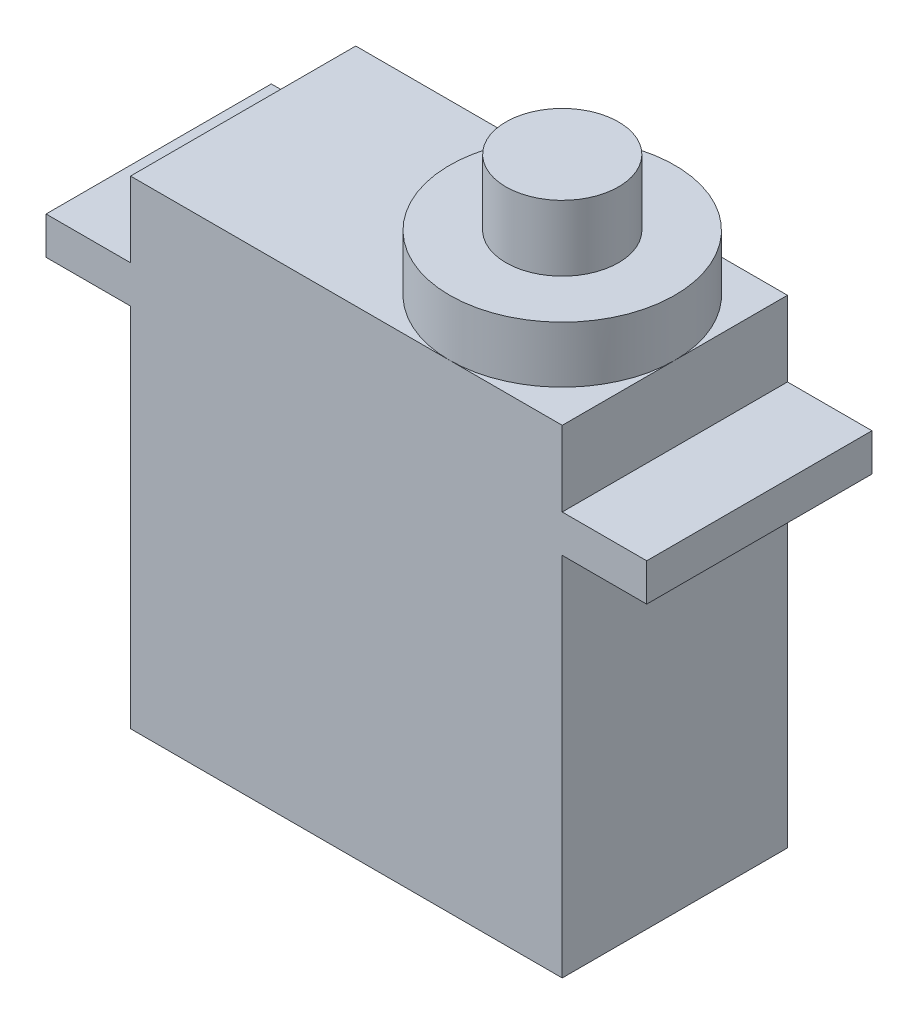
SolidWorks part; units mm, degrees
ref_plane "Front Plane" through (0, 0, 0) normal (0, 0, 1) x (1, 0, 0)
ref_plane "Top Plane" through (0, 0, 0) normal (0, 1, 0) x (1, 0, 0)
ref_plane "Right Plane" through (0, 0, 0) normal (1, 0, 0) x (0, 0, -1)
sketch "Sketch1" plane through (0, 0, 0) normal (0, 1, 0) x (1, 0, 0)
  line L1 (0, 0) -> (23, 0)
  line L2 (0, 0) -> (0, 12)
  line L3 (0, 12) -> (23, 12)
  line L4 (23, 0) -> (23, 12)
extrude "Boss-Extrude1" add sketch "Sketch1" along normal blind 19.5
sketch "Sketch2" plane through (0, 19.5, 0) normal (0, 1, 0) x (1, 0, 0)
  line L0 (11.5, 0) -> (-4.5, 0)
  line L1 (0, 0) -> (23, 0) construction
  line L2 (-4.5, 0) -> (-4.5, 12)
  line L3 (-4.5, 12) -> (27.5, 12)
  line L4 (27.5, 12) -> (27.5, 0)
  line L5 (27.5, 0) -> (0, 0)
  line M1 (0, 12) -> (0, 0)
  line M2 (0, 0) -> (23, 0)
  line M3 (23, 0) -> (23, 12)
  line M4 (23, 12) -> (0, 12)
extrude "Boss-Extrude2" add sketch "Sketch2" along normal blind 2 contours L3 L2 L0 M1 | L5 L4 L3 M3 | M4 M1 M2 M3
sketch "Sketch3" plane through (0, 21.5, 0) normal (0, 1, 0) x (1, 0, 0)
  line L1 (0, 0) -> (23, 0)
  line L2 (0, 0) -> (0, 12)
  line L3 (0, 12) -> (23, 12)
  line L4 (23, 0) -> (23, 12)
extrude "Boss-Extrude3" add sketch "Sketch3" along normal blind 4
sketch "Sketch4" plane through (0, 25.5, 0) normal (0, 1, 0) x (1, 0, 0)
  line L0 (23, 0) -> (11, 0)
  line L1 (0, 0) -> (23, 0) construction
  line L2 (11, 0) -> (11, 12)
  line L3 (23, 12) -> (0, 12) construction
  line L4 (11, 12) -> (23, 12)
  line L5 (23, 12) -> (11, 0)
  circle A0 centre (17, 6) radius 6
extrude "Boss-Extrude4" add sketch "Sketch4" along normal blind 3 contours A0 L5 | L5 A0
sketch "Sketch5" plane through (0, 28.5, 0) normal (0, 1, 0) x (1, 0, 0)
  circle A0 centre (17, 6) radius 3
extrude "Boss-Extrude5" add sketch "Sketch5" along normal blind 3.5
